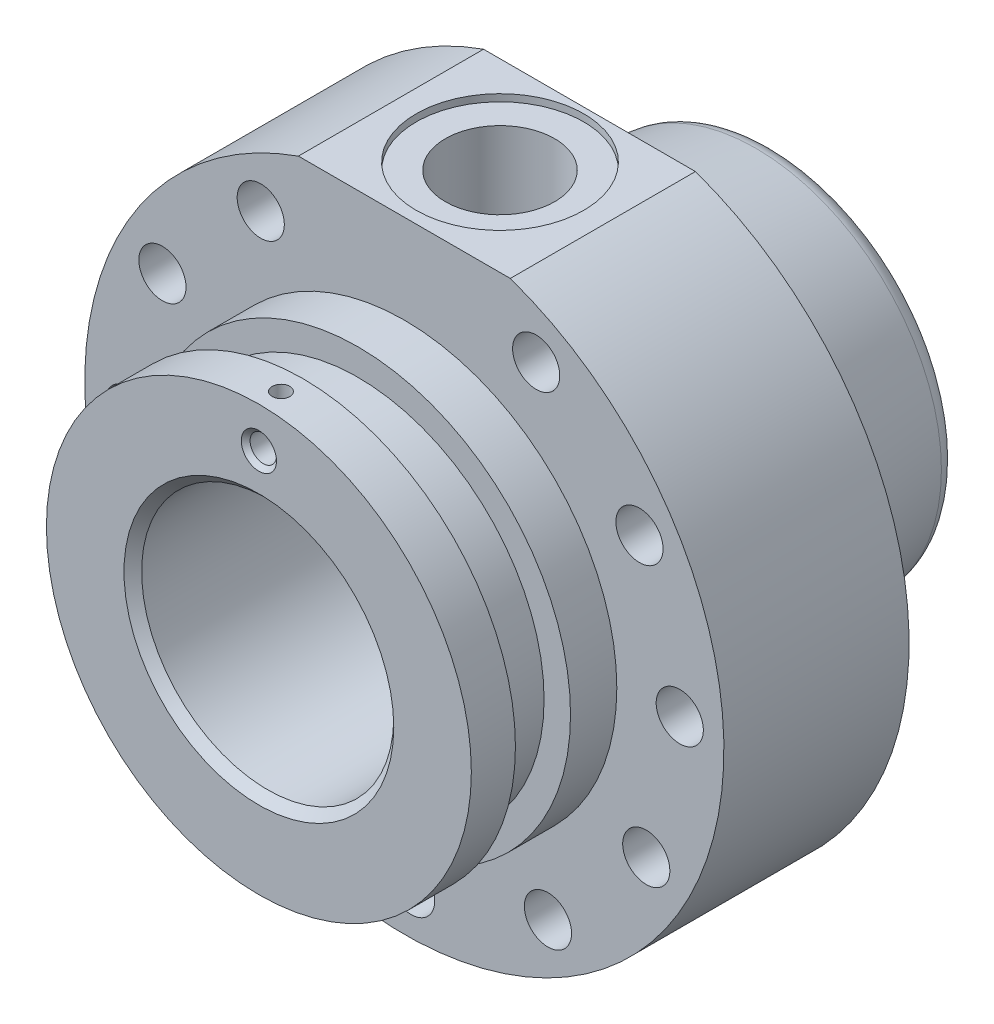
SolidWorks part; units mm, degrees
ref_plane "Front Plane" through (0, 0, 0) normal (0, 0, 1) x (1, 0, 0)
ref_plane "Top Plane" through (0, 0, 0) normal (0, 1, 0) x (1, 0, 0)
ref_plane "Right Plane" through (0, 0, 0) normal (1, 0, 0) x (0, 0, -1)
sketch "Sketch1" plane through (0, 0, 0) normal (0, 0, 1) x (1, 0, 0)
  circle A0 centre (0, 0) radius 72.5
  dimension "D1" = 145
extrude "Boss-Extrude1" add sketch "Sketch1" along normal blind 42
sketch "Sketch2" plane through (0, 0, 42) normal (0, 0, 1) x (1, 0, 0)
  circle A0 centre (0, 0) radius 48.2
  dimension "D1" = 96.4
extrude "Boss-Extrude2" add sketch "Sketch2" along normal blind 33
sketch "Sketch3" plane through (0, 0, 0) normal (1, 0, 0) x (0, 0, -1)
  line L0 (0, 47.6) -> (42, 41.5)
  line L1 (0, -72.5) -> (0, 72.5) construction
  line L2 (42, 41.5) -> (42, 28.6)
  line L3 (42, 28.6) -> (0, 28.6)
  line L4 (0, 0) -> (84.0613, 0) construction
  line L5 (0, 47.6) -> (0, 28.6)
  dimension "D1" = 47.6
  dimension "D2" = 28.6
  dimension "D3" = 41.5
  dimension "D4" = 42
revolve "Revolve1" add sketch "Sketch3" angle 360 about L4
sketch "Sketch4" plane through (0, 0, 75) normal (0, 0, 1) x (1, 0, 0)
  circle A0 centre (0, 0) radius 28.6
extrude "Cut-Extrude1" cut sketch "Sketch4" against normal through all
sketch "Sketch5" plane through (0, 0, -42) normal (0, 0, -1) x (-1, 0, 0)
  circle A0 centre (0, 0) radius 35
  dimension "D1" = 70
extrude "Cut-Extrude2" cut sketch "Sketch5" against normal blind 8
sketch "Sketch6" plane through (0, 0, 0) normal (1, 0, 0) x (0, 0, -1)
  line L0 (-75, 0) -> (0, 0) construction
  line L1 (-75, 48.2) -> (-75, -48.2) construction
  line L2 (0, -47.6) -> (0, 47.6) construction
  line L3 (-42, 48.2) -> (-75, 48.2) construction
  line L4 (-65, 48.2) -> (-52.5, 48.2)
  line L5 (-65, 48.2) -> (-65, 42.2)
  line L6 (-65, 42.2) -> (-52.5, 42.2)
  line L7 (-52.5, 48.2) -> (-52.5, 42.2)
  dimension "D1" = 6
  dimension "D2" = 10
  dimension "D3" = 12.5
revolve "Cut-Revolve1" cut sketch "Sketch6" angle 360 about L0
fillet "Fillet1" radius 5 1 edges at (41.5, 0, -42)
sketch "Sketch7" plane through (0, 0, 42) normal (0, 0, 1) x (1, 0, 0)
  circle A0 centre (0, 0) radius 62.5 construction
  circle A1 centre (-1.5443, 62.4809) radius 5.35
  dimension "D1" = 125
  dimension "D2" = 10.7
extrude "Cut-Extrude3" cut sketch "Sketch7" against normal through all
pattern_circular "CirPattern1" count 12 over 360 about axis through (0, 0, 0) along (0, 0, 1) of "Cut-Extrude3"
chamfer "Chamfer1" distance 2 angle 45 1 edges at (28.6, 0, 75)
ref_plane "Plane1" through (0, 70, 0) normal (0, 1, 0) x (1, 0, 0)
sketch "Sketch8" plane through (0, 70, 0) normal (0, 1, 0) x (1, 0, 0)
  line L1 (-25.5, 7.8464) -> (25.5, 7.8464)
  line L2 (-25.5, 7.8464) -> (-25.5, -49.2121)
  line L3 (-25.5, -49.2121) -> (25.5, -49.2121)
  line L4 (25.5, 7.8464) -> (25.5, -49.2121)
  line L5 (-25.5, 7.8464) -> (25.5, -49.2121) construction
  line L6 (-25.5, -49.2121) -> (25.5, 7.8464) construction
  point P0 (0, -20.6829)
  dimension "D1" = 51
extrude "Cut-Extrude4" cut sketch "Sketch8" against normal blind 1.6 and the other way blind 22
sketch "Sketch9" plane through (0, 68.4, 0) normal (0, 1, 0) x (1, 0, 0)
  circle A0 centre (0, -20.3026) radius 19
extrude "Cut-Extrude5" cut sketch "Sketch9" against normal blind 1.6
sketch "Sketch10" plane through (0, 0, 42) normal (0, 0, 1) x (1, 0, 0)
  circle A0 centre (-1.5443, 62.4809) radius 5.35 construction
  circle A1 centre (-1.5443, 62.4809) radius 5.35
extrude "Boss-Extrude3" add sketch "Sketch10" against normal blind 42
sketch "Sketch11" plane through (0, 66.8, 0) normal (0, 1, 0) x (1, 0, 0)
  circle A0 centre (0, -20.3026) radius 12.4
extrude "Cut-Extrude6" cut sketch "Sketch11" against normal blind 23
sketch "Sketch12" plane through (0, 66.8, 0) normal (0, 1, 0) x (1, 0, 0)
  circle A0 centre (0, -20.3026) radius 19
extrude "Cut-Extrude7" cut sketch "Sketch12" along normal blind 23
sketch "Sketch13" plane through (0, 43.8, 0) normal (0, 1, 0) x (1, 0, 0)
  circle A0 centre (0, -20.3026) radius 7.5
extrude "Cut-Extrude8" cut sketch "Sketch13" against normal blind 23
sketch "Sketch14" plane through (0, 0, 75) normal (0, 0, 1) x (1, 0, 0)
  circle A0 centre (0, 39) radius 3
  dimension "D1" = 39
extrude "Cut-Extrude9" cut sketch "Sketch14" against normal up to surface (47.8235 mm away)
chamfer "Chamfer2" distance 1 angle 45 1 edges at (3, 39, 75)
sketch "Sketch15" plane through (0, 0, 0) normal (0, 1, 0) x (1, 0, 0)
  line L0 (-48.2, -75) -> (48.2, -75) construction
  circle A0 centre (0, -70) radius 2
  dimension "D1" = 4
  dimension "D2" = 5
extrude "Cut-Extrude10" cut sketch "Sketch15" along normal through all from offset 40
